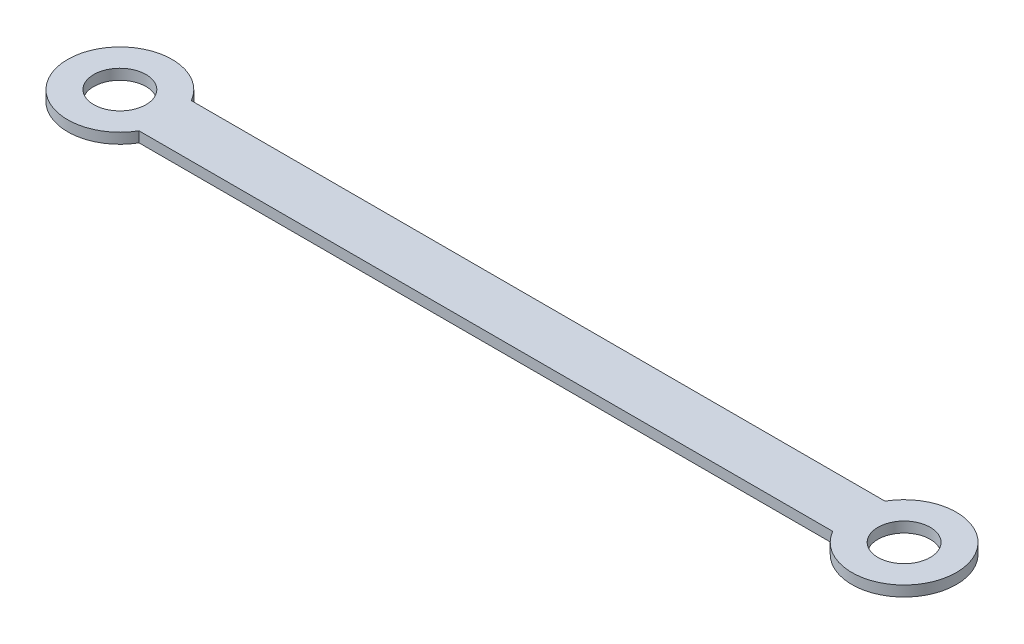
SolidWorks part; units mm, degrees
ref_plane "前基準面" through (0, 0, 0) normal (0, 0, 1) x (1, 0, 0)
ref_plane "上基準面" through (0, 0, 0) normal (0, 1, 0) x (1, 0, 0)
ref_plane "右基準面" through (0, 0, 0) normal (1, 0, 0) x (0, 0, -1)
sketch "草圖5" plane through (0, 0, 0) normal (0, 1, 0) x (1, 0, 0)
  line L0 (8.6603, -5) -> (141.3397, -5)
  line L2 (141.3397, 5) -> (8.6603, 5)
  circle A0 centre (0, 0) radius 5
  arc A1 (8.6603, 5) -> (8.6603, -5) centre (0, 0) ccw
  arc A2 (141.3397, -5) -> (141.3397, 5) centre (150, 0) ccw
  circle A3 centre (150, 0) radius 5
  dimension "D1" = 10
  dimension "D2" = 10
  dimension "D3" = 10
  dimension "D4" = 150
extrude "填料-伸長1" add sketch "草圖5" along normal blind 2
